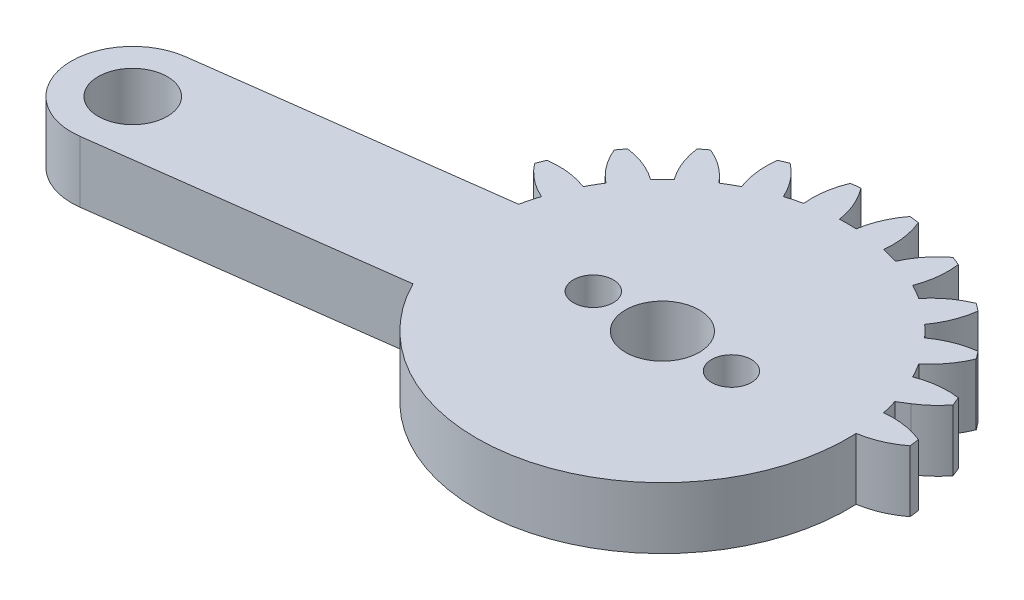
SolidWorks part; units mm, degrees
ref_plane "Front Plane" through (0, 0, 0) normal (0, 0, 1) x (1, 0, 0)
ref_plane "Top Plane" through (0, 0, 0) normal (0, 1, 0) x (1, 0, 0)
ref_plane "Right Plane" through (0, 0, 0) normal (1, 0, 0) x (0, 0, -1)
sketch "Sketch1" plane through (0, 0, 0) normal (0, 1, 0) x (1, 0, 0)
  line L0 (20.6437, 4) -> (2.0816, 4)
  line L1 (2.0816, -4) -> (20.6437, -4)
  arc A0 (2.0816, 4) -> (3.5217, 5.3071) centre (-0.7683, 8.5867) ccw
  arc A1 (3.5217, 5.3071) -> (3.2829, 5.8838) centre (-10.1063, 0) ccw
  arc A2 (3.2829, 5.8838) -> (0.6271, 5.5703) centre (2.5684, 0.5313) ccw
  arc A3 (0.6271, 5.5703) -> (0.0844, 6.5103) centre (-10.1063, 0) ccw
  arc A4 (0.0844, 6.5103) -> (1.6838, 8.6535) centre (-3.3089, 10.711) ccw
  arc A5 (1.6838, 8.6535) -> (1.3038, 9.1487) centre (-10.1063, 0) ccw
  arc A6 (1.3038, 9.1487) -> (-1.1803, 8.1585) centre (1.999, 3.7936) ccw
  arc A7 (-1.1803, 8.1585) -> (-1.9479, 8.926) centre (-10.1063, 0) ccw
  arc A8 (-1.9479, 8.926) -> (-0.9576, 11.4102) centre (-6.3127, 12.1053) ccw
  arc A9 (-0.9576, 11.4102) -> (-1.4528, 11.7901) centre (-10.1063, 0) ccw
  arc A10 (-1.4528, 11.7901) -> (-3.596, 10.1907) centre (0.6046, 6.7975) ccw
  arc A11 (-3.596, 10.1907) -> (-4.5361, 10.7334) centre (-10.1063, 0) ccw
  arc A12 (-4.5361, 10.7334) -> (-4.2225, 13.3892) centre (-9.5751, 12.6747) ccw
  arc A13 (-4.2225, 13.3892) -> (-4.7992, 13.6281) centre (-10.1063, 0) ccw
  arc A14 (-4.7992, 13.6281) -> (-6.4554, 11.5285) centre (-1.5196, 9.3381) ccw
  arc A15 (-6.4554, 11.5285) -> (-7.5039, 11.8094) centre (-10.1063, 0) ccw
  arc A16 (-7.5039, 11.8094) -> (-7.8884, 14.4558) centre (-12.8736, 12.3803) ccw
  arc A17 (-7.8884, 14.4558) -> (-8.5072, 14.5373) centre (-10.1063, 0) ccw
  arc A18 (-8.5072, 14.5373) -> (-9.5636, 12.0806) centre (-4.2291, 11.2423) ccw
  arc A19 (-9.5636, 12.0806) -> (-10.6491, 12.0806) centre (-10.1063, 0) ccw
  arc A20 (-10.6491, 12.0806) -> (-11.7054, 14.5373) centre (-15.9836, 11.2423) ccw
  arc A21 (-11.7054, 14.5373) -> (-12.3243, 14.4558) centre (-10.1063, 0) ccw
  arc A22 (-12.3243, 14.4558) -> (-12.7088, 11.8094) centre (-7.3391, 12.3803) ccw
  arc A23 (-12.7088, 11.8094) -> (-13.7573, 11.5285) centre (-10.1063, 0) ccw
  arc A24 (-13.7573, 11.5285) -> (-15.4135, 13.6281) centre (-18.6931, 9.3381) ccw
  arc A25 (-15.4135, 13.6281) -> (-15.9901, 13.3892) centre (-10.1063, 0) ccw
  arc A26 (-15.9901, 13.3892) -> (-15.6766, 10.7334) centre (-10.6376, 12.6747) ccw
  arc A27 (-15.6766, 10.7334) -> (-16.6166, 10.1907) centre (-10.1063, 0) ccw
  arc A28 (-16.6166, 10.1907) -> (-18.7599, 11.7901) centre (-20.8173, 6.7975) ccw
  arc A29 (-18.7599, 11.7901) -> (-19.255, 11.4102) centre (-10.1063, 0) ccw
  arc A30 (-19.255, 11.4102) -> (-18.2648, 8.926) centre (-13.9, 12.1053) ccw
  arc A31 (-18.2648, 8.926) -> (-19.0324, 8.1585) centre (-10.1063, 0) ccw
  arc A32 (-19.0324, 8.1585) -> (-21.5165, 9.1487) centre (-22.2117, 3.7936) ccw
  arc A33 (-21.5165, 9.1487) -> (-21.8965, 8.6535) centre (-10.1063, 0) ccw
  arc A34 (-21.8965, 8.6535) -> (-20.2971, 6.5103) centre (-16.9038, 10.711) ccw
  arc A35 (-20.2971, 6.5103) -> (-20.8398, 5.5703) centre (-10.1063, 0) ccw
  arc A36 (-20.8398, 5.5703) -> (-23.4956, 5.8838) centre (-22.7811, 0.5313) ccw
  arc A37 (-23.4956, 5.8838) -> (-23.7344, 5.3071) centre (-10.1063, 0) ccw
  arc A38 (-23.7344, 5.3071) -> (-21.6348, 3.6509) centre (-19.4444, 8.5867) ccw
  arc A39 (-21.6348, 3.6509) -> (-21.9157, 2.6025) centre (-10.1063, 0) ccw
  arc A40 (-21.9157, 2.6025) -> (-24.5622, 2.2179) centre (-22.4867, -2.7673) ccw
  arc A41 (-24.5622, 2.2179) -> (-24.6437, 1.5991) centre (-10.1063, 0) ccw
  arc A42 (-24.6437, 1.5991) -> (-22.1869, 0.5427) centre (-21.3486, 5.8773) ccw
  arc A43 (-22.1869, 0.5427) -> (-22.1869, -0.5427) centre (-10.1063, 0) ccw
  arc A44 (-22.1869, -0.5427) -> (-24.6437, -1.5991) centre (-21.3486, -5.8773) ccw
  arc A45 (-24.6437, -1.5991) -> (-24.5622, -2.2179) centre (-10.1063, 0) ccw
  arc A46 (-24.5622, -2.2179) -> (-21.9157, -2.6025) centre (-22.4867, 2.7673) ccw
  arc A47 (-21.9157, -2.6025) -> (-21.6348, -3.6509) centre (-10.1063, 0) ccw
  arc A48 (-21.6348, -3.6509) -> (-23.7344, -5.3071) centre (-19.4444, -8.5867) ccw
  arc A49 (-23.7344, -5.3071) -> (-23.4956, -5.8838) centre (-10.1063, 0) ccw
  arc A50 (-23.4956, -5.8838) -> (-20.8398, -5.5703) centre (-22.7811, -0.5313) ccw
  arc A51 (-20.8398, -5.5703) -> (-20.2971, -6.5103) centre (-10.1063, 0) ccw
  arc A52 (-20.2971, -6.5103) -> (-21.8965, -8.6535) centre (-16.9038, -10.711) ccw
  arc A53 (-21.8965, -8.6535) -> (-21.5165, -9.1487) centre (-10.1063, 0) ccw
  arc A54 (-21.5165, -9.1487) -> (-19.0324, -8.1585) centre (-22.2117, -3.7936) ccw
  arc A55 (-19.0324, -8.1585) -> (-18.2648, -8.926) centre (-10.1063, 0) ccw
  arc A56 (-18.2648, -8.926) -> (-19.255, -11.4102) centre (-13.9, -12.1053) ccw
  arc A57 (-19.255, -11.4102) -> (-18.7599, -11.7901) centre (-10.1063, 0) ccw
  arc A58 (-18.7599, -11.7901) -> (-16.6166, -10.1907) centre (-20.8173, -6.7975) ccw
  arc A59 (-16.6166, -10.1907) -> (-15.6766, -10.7334) centre (-10.1063, 0) ccw
  arc A60 (-15.6766, -10.7334) -> (-15.9901, -13.3892) centre (-10.6376, -12.6747) ccw
  arc A61 (-15.9901, -13.3892) -> (-15.4135, -13.6281) centre (-10.1063, 0) ccw
  arc A62 (-15.4135, -13.6281) -> (-13.7573, -11.5285) centre (-18.6931, -9.3381) ccw
  arc A63 (-13.7573, -11.5285) -> (-12.7088, -11.8094) centre (-10.1063, 0) ccw
  arc A64 (-12.7088, -11.8094) -> (-12.3243, -14.4558) centre (-7.3391, -12.3803) ccw
  arc A65 (-12.3243, -14.4558) -> (-11.7054, -14.5373) centre (-10.1063, 0) ccw
  arc A66 (-11.7054, -14.5373) -> (-10.6491, -12.0806) centre (-15.9836, -11.2423) ccw
  arc A67 (-10.6491, -12.0806) -> (-9.5636, -12.0806) centre (-10.1063, 0) ccw
  arc A68 (-9.5636, -12.0806) -> (-8.5072, -14.5373) centre (-4.2291, -11.2423) ccw
  arc A69 (-8.5072, -14.5373) -> (-7.8884, -14.4558) centre (-10.1063, 0) ccw
  arc A70 (-7.8884, -14.4558) -> (-7.5039, -11.8094) centre (-12.8736, -12.3803) ccw
  arc A71 (-7.5039, -11.8094) -> (-6.4554, -11.5285) centre (-10.1063, 0) ccw
  arc A72 (-6.4554, -11.5285) -> (-4.7992, -13.6281) centre (-1.5196, -9.3381) ccw
  arc A73 (-4.7992, -13.6281) -> (-4.2225, -13.3892) centre (-10.1063, 0) ccw
  arc A74 (-4.2225, -13.3892) -> (-4.5361, -10.7334) centre (-9.5751, -12.6747) ccw
  arc A75 (-4.5361, -10.7334) -> (-3.596, -10.1907) centre (-10.1063, 0) ccw
  arc A76 (-3.596, -10.1907) -> (-1.4528, -11.7901) centre (0.6046, -6.7975) ccw
  arc A77 (-1.4528, -11.7901) -> (-0.9576, -11.4102) centre (-10.1063, 0) ccw
  arc A78 (-0.9576, -11.4102) -> (-1.9479, -8.926) centre (-6.3127, -12.1053) ccw
  arc A79 (-1.9479, -8.926) -> (-1.1803, -8.1585) centre (-10.1063, 0) ccw
  arc A80 (-1.1803, -8.1585) -> (1.3038, -9.1487) centre (1.999, -3.7936) ccw
  arc A81 (1.3038, -9.1487) -> (1.6838, -8.6535) centre (-10.1063, 0) ccw
  arc A82 (1.6838, -8.6535) -> (0.0844, -6.5103) centre (-3.3089, -10.711) ccw
  arc A83 (0.0844, -6.5103) -> (0.6271, -5.5703) centre (-10.1063, 0) ccw
  arc A84 (0.6271, -5.5703) -> (3.2829, -5.8838) centre (2.5684, -0.5313) ccw
  arc A85 (3.2829, -5.8838) -> (3.5217, -5.3071) centre (-10.1063, 0) ccw
  arc A86 (3.5217, -5.3071) -> (2.0816, -4) centre (-0.7683, -8.5867) ccw
  arc A87 (20.6437, -4) -> (20.6437, 4) centre (20.6437, 0) ccw
  circle A88 centre (-10.1063, 0) radius 1.5
  circle A89 centre (20.6437, 0) radius 2.25
  dimension "D1" = 3
  dimension "D2" = 4.5
extrude "Boss-Extrude1" add sketch "Sketch1" along normal blind 4
sketch "Sketch3" plane through (0, 4, 0) normal (0, 1, 0) x (1, 0, 0)
  line L0 (-10.1063, 0) -> (-40.8563, 0) construction
  line L1 (-10.1063, 0) -> (-40.5933, -4.0137)
  line L2 (-10.6284, 3.9658) -> (-41.1154, -0.0479)
  line L3 (-9.5842, -3.9658) -> (-40.0712, -7.9795)
  line L4 (-10.1063, 0) -> (-4.5096, 13.5117) construction
  line L5 (-10.1063, 0) -> (-8.1974, 14.4999) construction
  circle A0 centre (-10.1063, 0) radius 1.5
  circle A1 centre (20.6437, 0) radius 2.25 construction
  circle A2 centre (20.6437, 0) radius 2.25
  circle A3 centre (-40.5933, -4.0137) radius 2.25
  circle A4 centre (-40.5933, -4.0137) radius 4
  circle A5 centre (-10.1063, 0) radius 4
  arc A6 (-4.2225, 13.3892) -> (-4.7992, 13.6281) centre (-10.1063, 0) ccw construction
  arc A7 (-7.8884, 14.4558) -> (-8.5072, 14.5373) centre (-10.1063, 0) ccw construction
  dimension "D2" = 3
  dimension "D5" = 4.5
  dimension "D6" = 8
  dimension "D7" = 8
  dimension "D1" = 30.75
  dimension "D4" = 7.5
extrude "Boss-Extrude2" add sketch "Sketch3" against normal blind 4
sketch "Sketch4" plane through (0, 4, 0) normal (0, 1, 0) x (1, 0, 0)
  line L0 (20.6437, 4) -> (2.0816, 4) construction
  line L1 (2.0816, -4) -> (20.6437, -4) construction
  line L2 (20.6437, 4) -> (2.0816, 4)
  line L3 (2.0816, -4) -> (20.6437, -4)
  line L4 (2.0816, 4) -> (1.4381, 3.6001)
  line L5 (-21.6245, -5.5509) -> (-20.8986, -5.4553)
  line L6 (-10.1063, 0) -> (0.0844, 6.5103) construction
  line L7 (-10.1063, 0) -> (1.9742, 0.5427) construction
  line L8 (-24.5755, 2.1296) -> (-41.1154, -0.0479)
  line L9 (-40.0712, -7.9795) -> (-23.5312, -5.8019)
  line L10 (2.0816, -4) -> (20.6437, -4)
  line L11 (20.6437, 4) -> (2.0816, 4)
  line L12 (-21.9429, 2.4762) -> (-41.1154, -0.0479)
  line L13 (-40.0712, -7.9795) -> (-21.6245, -5.5509)
  line L14 (2.0816, -4) -> (20.6437, -4)
  line L15 (20.6437, 4) -> (2.0816, 4)
  circle A0 centre (-10.1063, 0) radius 12.0927
  arc A1 (3.2829, 5.8838) -> (0.6271, 5.5703) centre (2.5684, 0.5313) ccw construction
  arc A2 (3.5217, 5.3071) -> (3.2829, 5.8838) centre (-10.1063, 0) ccw construction
  arc A3 (2.0816, 4) -> (3.5217, 5.3071) centre (-0.7683, 8.5867) ccw construction
  arc A4 (20.6437, -4) -> (20.6437, 4) centre (20.6437, 0) ccw construction
  arc A5 (3.5217, -5.3071) -> (2.0816, -4) centre (-0.7683, -8.5867) ccw construction
  arc A6 (3.2829, -5.8838) -> (3.5217, -5.3071) centre (-10.1063, 0) ccw construction
  arc A7 (0.6271, -5.5703) -> (3.2829, -5.8838) centre (2.5684, -0.5313) ccw construction
  arc A8 (3.2829, 5.8838) -> (0.6271, 5.5703) centre (2.5684, 0.5313) ccw
  arc A9 (3.5217, 5.3071) -> (3.2829, 5.8838) centre (-10.1063, 0) ccw
  arc A10 (2.0816, 4) -> (3.5217, 5.3071) centre (-0.7683, 8.5867) ccw
  arc A11 (20.6437, -4) -> (20.6437, 4) centre (20.6437, 0) ccw
  arc A12 (3.5217, -5.3071) -> (2.0816, -4) centre (-0.7683, -8.5867) ccw
  arc A13 (3.2829, -5.8838) -> (3.5217, -5.3071) centre (-10.1063, 0) ccw
  arc A14 (0.6271, -5.5703) -> (3.2829, -5.8838) centre (2.5684, -0.5313) ccw
  arc A15 (1.9742, 0.5427) -> (4.431, 1.5991) centre (1.1359, 5.8773) ccw
  arc A16 (4.3495, 2.2179) -> (1.7031, 2.6025) centre (2.274, -2.7673) ccw
  arc A17 (4.431, 1.5991) -> (4.3495, 2.2179) centre (-10.1063, 0) ccw
  arc A95 (-21.6348, 3.6509) -> (-21.9157, 2.6025) centre (-10.1063, 0) ccw
  arc A96 (-41.1154, -0.0479) -> (-40.0712, -7.9795) centre (-40.5933, -4.0137) ccw
  arc A97 (-20.2971, -6.5103) -> (-21.8965, -8.6535) centre (-16.9038, -10.711) ccw
  arc A98 (-21.8965, -8.6535) -> (-21.5165, -9.1487) centre (-10.1063, 0) ccw
  arc A99 (-21.5165, -9.1487) -> (-19.0324, -8.1585) centre (-22.2117, -3.7936) ccw
  arc A100 (-19.0324, -8.1585) -> (-18.2648, -8.926) centre (-10.1063, 0) ccw
  arc A101 (-18.2648, -8.926) -> (-19.255, -11.4102) centre (-13.9, -12.1053) ccw
  arc A102 (-19.255, -11.4102) -> (-18.7599, -11.7901) centre (-10.1063, 0) ccw
  arc A103 (-18.7599, -11.7901) -> (-16.6166, -10.1907) centre (-20.8173, -6.7975) ccw
  arc A104 (-16.6166, -10.1907) -> (-15.6766, -10.7334) centre (-10.1063, 0) ccw
  arc A105 (-15.6766, -10.7334) -> (-15.9901, -13.3892) centre (-10.6376, -12.6747) ccw
  arc A106 (-15.9901, -13.3892) -> (-15.4135, -13.6281) centre (-10.1063, 0) ccw
  arc A107 (-15.4135, -13.6281) -> (-13.7573, -11.5285) centre (-18.6931, -9.3381) ccw
  arc A108 (-13.7573, -11.5285) -> (-12.7088, -11.8094) centre (-10.1063, 0) ccw
  arc A109 (-12.7088, -11.8094) -> (-12.3243, -14.4558) centre (-7.3391, -12.3803) ccw
  arc A110 (-12.3243, -14.4558) -> (-11.7054, -14.5373) centre (-10.1063, 0) ccw
  arc A111 (-11.7054, -14.5373) -> (-10.6491, -12.0806) centre (-15.9836, -11.2423) ccw
  arc A112 (-10.6491, -12.0806) -> (-9.5636, -12.0806) centre (-10.1063, 0) ccw
  arc A113 (-9.5636, -12.0806) -> (-8.5072, -14.5373) centre (-4.2291, -11.2423) ccw
  arc A114 (-8.5072, -14.5373) -> (-7.8884, -14.4558) centre (-10.1063, 0) ccw
  arc A115 (-7.8884, -14.4558) -> (-7.5039, -11.8094) centre (-12.8736, -12.3803) ccw
  arc A116 (-7.5039, -11.8094) -> (-6.4554, -11.5285) centre (-10.1063, 0) ccw
  arc A117 (-6.4554, -11.5285) -> (-4.7992, -13.6281) centre (-1.5196, -9.3381) ccw
  arc A118 (-4.7992, -13.6281) -> (-4.2225, -13.3892) centre (-10.1063, 0) ccw
  arc A119 (-4.2225, -13.3892) -> (-4.5361, -10.7334) centre (-9.5751, -12.6747) ccw
  arc A120 (-4.5361, -10.7334) -> (-3.596, -10.1907) centre (-10.1063, 0) ccw
  arc A121 (-3.596, -10.1907) -> (-1.4528, -11.7901) centre (0.6046, -6.7975) ccw
  arc A122 (-1.4528, -11.7901) -> (-0.9576, -11.4102) centre (-10.1063, 0) ccw
  arc A123 (-0.9576, -11.4102) -> (-1.9479, -8.926) centre (-6.3127, -12.1053) ccw
  arc A124 (-1.9479, -8.926) -> (-1.1803, -8.1585) centre (-10.1063, 0) ccw
  arc A125 (-1.1803, -8.1585) -> (1.3038, -9.1487) centre (1.999, -3.7936) ccw
  arc A126 (1.3038, -9.1487) -> (1.6838, -8.6535) centre (-10.1063, 0) ccw
  arc A127 (1.6838, -8.6535) -> (0.0844, -6.5103) centre (-3.3089, -10.711) ccw
  arc A128 (0.0844, -6.5103) -> (0.6271, -5.5703) centre (-10.1063, 0) ccw
  arc A129 (0.6271, -5.5703) -> (3.2829, -5.8838) centre (2.5684, -0.5313) ccw
  arc A130 (3.2829, -5.8838) -> (3.5217, -5.3071) centre (-10.1063, 0) ccw
  arc A131 (3.5217, -5.3071) -> (2.0816, -4) centre (-0.7683, -8.5867) ccw
  arc A132 (20.6437, -4) -> (20.6437, 4) centre (20.6437, 0) ccw
  arc A133 (2.0816, 4) -> (3.5217, 5.3071) centre (-0.7683, 8.5867) ccw
  arc A134 (3.5217, 5.3071) -> (3.2829, 5.8838) centre (-10.1063, 0) ccw
  arc A135 (3.2829, 5.8838) -> (0.6271, 5.5703) centre (2.5684, 0.5313) ccw
  arc A136 (0.6271, 5.5703) -> (0.0844, 6.5103) centre (-10.1063, 0) ccw
  arc A137 (0.0844, 6.5103) -> (1.6838, 8.6535) centre (-3.3089, 10.711) ccw
  arc A138 (1.6838, 8.6535) -> (1.3038, 9.1487) centre (-10.1063, 0) ccw
  arc A139 (1.3038, 9.1487) -> (-1.1803, 8.1585) centre (1.999, 3.7936) ccw
  arc A140 (-1.1803, 8.1585) -> (-1.9479, 8.926) centre (-10.1063, 0) ccw
  arc A141 (-1.9479, 8.926) -> (-0.9576, 11.4102) centre (-6.3127, 12.1053) ccw
  arc A142 (-0.9576, 11.4102) -> (-1.4528, 11.7901) centre (-10.1063, 0) ccw
  arc A143 (-1.4528, 11.7901) -> (-3.596, 10.1907) centre (0.6046, 6.7975) ccw
  arc A144 (-3.596, 10.1907) -> (-4.5361, 10.7334) centre (-10.1063, 0) ccw
  arc A145 (-4.5361, 10.7334) -> (-4.2225, 13.3892) centre (-9.5751, 12.6747) ccw
  arc A146 (-4.2225, 13.3892) -> (-4.7992, 13.6281) centre (-10.1063, 0) ccw
  arc A147 (-4.7992, 13.6281) -> (-6.4554, 11.5285) centre (-1.5196, 9.3381) ccw
  arc A148 (-6.4554, 11.5285) -> (-7.5039, 11.8094) centre (-10.1063, 0) ccw
  arc A149 (-7.5039, 11.8094) -> (-7.8884, 14.4558) centre (-12.8736, 12.3803) ccw
  arc A150 (-7.8884, 14.4558) -> (-8.5072, 14.5373) centre (-10.1063, 0) ccw
  arc A151 (-8.5072, 14.5373) -> (-9.5636, 12.0806) centre (-4.2291, 11.2423) ccw
  arc A152 (-9.5636, 12.0806) -> (-10.6491, 12.0806) centre (-10.1063, 0) ccw
  arc A153 (-10.6491, 12.0806) -> (-11.7054, 14.5373) centre (-15.9836, 11.2423) ccw
  arc A154 (-11.7054, 14.5373) -> (-12.3243, 14.4558) centre (-10.1063, 0) ccw
  arc A155 (-12.3243, 14.4558) -> (-12.7088, 11.8094) centre (-7.3391, 12.3803) ccw
  arc A156 (-12.7088, 11.8094) -> (-13.7573, 11.5285) centre (-10.1063, 0) ccw
  arc A157 (-13.7573, 11.5285) -> (-15.4135, 13.6281) centre (-18.6931, 9.3381) ccw
  arc A158 (-15.4135, 13.6281) -> (-15.9901, 13.3892) centre (-10.1063, 0) ccw
  arc A159 (-15.9901, 13.3892) -> (-15.6766, 10.7334) centre (-10.6376, 12.6747) ccw
  arc A160 (-15.6766, 10.7334) -> (-16.6166, 10.1907) centre (-10.1063, 0) ccw
  arc A161 (-16.6166, 10.1907) -> (-18.7599, 11.7901) centre (-20.8173, 6.7975) ccw
  arc A162 (-18.7599, 11.7901) -> (-19.255, 11.4102) centre (-10.1063, 0) ccw
  arc A163 (-19.255, 11.4102) -> (-18.2648, 8.926) centre (-13.9, 12.1053) ccw
  arc A164 (-18.2648, 8.926) -> (-19.0324, 8.1585) centre (-10.1063, 0) ccw
  arc A165 (-19.0324, 8.1585) -> (-21.5165, 9.1487) centre (-22.2117, 3.7936) ccw
  arc A166 (-21.5165, 9.1487) -> (-21.8965, 8.6535) centre (-10.1063, 0) ccw
  arc A167 (-21.8965, 8.6535) -> (-20.2971, 6.5103) centre (-16.9038, 10.711) ccw
  arc A168 (-20.2971, 6.5103) -> (-20.8398, 5.5703) centre (-10.1063, 0) ccw
  arc A169 (-20.8398, 5.5703) -> (-23.4956, 5.8838) centre (-22.7811, 0.5313) ccw
  arc A170 (-23.4956, 5.8838) -> (-23.7344, 5.3071) centre (-10.1063, 0) ccw
  arc A171 (-23.7344, 5.3071) -> (-21.6348, 3.6509) centre (-19.4444, 8.5867) ccw
  arc A172 (-21.6348, 3.6509) -> (-21.9157, 2.6025) centre (-10.1063, 0) ccw
  arc A175 (-23.4956, -5.8838) -> (-20.8398, -5.5703) centre (-22.7811, -0.5313) ccw
  arc A176 (-41.1154, -0.0479) -> (-40.0712, -7.9795) centre (-40.5933, -4.0137) ccw
  arc A177 (-20.2971, -6.5103) -> (-21.8965, -8.6535) centre (-16.9038, -10.711) ccw
  arc A178 (-21.8965, -8.6535) -> (-21.5165, -9.1487) centre (-10.1063, 0) ccw
  arc A179 (-21.5165, -9.1487) -> (-19.0324, -8.1585) centre (-22.2117, -3.7936) ccw
  arc A180 (-19.0324, -8.1585) -> (-18.2648, -8.926) centre (-10.1063, 0) ccw
  arc A181 (-18.2648, -8.926) -> (-19.255, -11.4102) centre (-13.9, -12.1053) ccw
  arc A182 (-19.255, -11.4102) -> (-18.7599, -11.7901) centre (-10.1063, 0) ccw
  arc A183 (-18.7599, -11.7901) -> (-16.6166, -10.1907) centre (-20.8173, -6.7975) ccw
  arc A184 (-16.6166, -10.1907) -> (-15.6766, -10.7334) centre (-10.1063, 0) ccw
  arc A185 (-15.6766, -10.7334) -> (-15.9901, -13.3892) centre (-10.6376, -12.6747) ccw
  arc A186 (-15.9901, -13.3892) -> (-15.4135, -13.6281) centre (-10.1063, 0) ccw
  arc A187 (-15.4135, -13.6281) -> (-13.7573, -11.5285) centre (-18.6931, -9.3381) ccw
  arc A188 (-13.7573, -11.5285) -> (-12.7088, -11.8094) centre (-10.1063, 0) ccw
  arc A189 (-12.7088, -11.8094) -> (-12.3243, -14.4558) centre (-7.3391, -12.3803) ccw
  arc A190 (-12.3243, -14.4558) -> (-11.7054, -14.5373) centre (-10.1063, 0) ccw
  arc A191 (-11.7054, -14.5373) -> (-10.6491, -12.0806) centre (-15.9836, -11.2423) ccw
  arc A192 (-10.6491, -12.0806) -> (-9.5636, -12.0806) centre (-10.1063, 0) ccw
  arc A193 (-9.5636, -12.0806) -> (-8.5072, -14.5373) centre (-4.2291, -11.2423) ccw
  arc A194 (-8.5072, -14.5373) -> (-7.8884, -14.4558) centre (-10.1063, 0) ccw
  arc A195 (-7.8884, -14.4558) -> (-7.5039, -11.8094) centre (-12.8736, -12.3803) ccw
  arc A196 (-7.5039, -11.8094) -> (-6.4554, -11.5285) centre (-10.1063, 0) ccw
  arc A197 (-6.4554, -11.5285) -> (-4.7992, -13.6281) centre (-1.5196, -9.3381) ccw
  arc A198 (-4.7992, -13.6281) -> (-4.2225, -13.3892) centre (-10.1063, 0) ccw
  arc A199 (-4.2225, -13.3892) -> (-4.5361, -10.7334) centre (-9.5751, -12.6747) ccw
  arc A200 (-4.5361, -10.7334) -> (-3.596, -10.1907) centre (-10.1063, 0) ccw
  arc A201 (-3.596, -10.1907) -> (-1.4528, -11.7901) centre (0.6046, -6.7975) ccw
  arc A202 (-1.4528, -11.7901) -> (-0.9576, -11.4102) centre (-10.1063, 0) ccw
  arc A203 (-0.9576, -11.4102) -> (-1.9479, -8.926) centre (-6.3127, -12.1053) ccw
  arc A204 (-1.9479, -8.926) -> (-1.1803, -8.1585) centre (-10.1063, 0) ccw
  arc A205 (-1.1803, -8.1585) -> (1.3038, -9.1487) centre (1.999, -3.7936) ccw
  arc A206 (1.3038, -9.1487) -> (1.6838, -8.6535) centre (-10.1063, 0) ccw
  arc A207 (1.6838, -8.6535) -> (0.0844, -6.5103) centre (-3.3089, -10.711) ccw
  arc A208 (0.0844, -6.5103) -> (0.6271, -5.5703) centre (-10.1063, 0) ccw
  arc A209 (0.6271, -5.5703) -> (3.2829, -5.8838) centre (2.5684, -0.5313) ccw
  arc A210 (3.2829, -5.8838) -> (3.5217, -5.3071) centre (-10.1063, 0) ccw
  arc A211 (3.5217, -5.3071) -> (2.0816, -4) centre (-0.7683, -8.5867) ccw
  arc A212 (20.6437, -4) -> (20.6437, 4) centre (20.6437, 0) ccw
  arc A213 (2.0816, 4) -> (3.5217, 5.3071) centre (-0.7683, 8.5867) ccw
  arc A214 (3.5217, 5.3071) -> (3.2829, 5.8838) centre (-10.1063, 0) ccw
  arc A215 (3.2829, 5.8838) -> (0.6271, 5.5703) centre (2.5684, 0.5313) ccw
  arc A216 (0.6271, 5.5703) -> (0.0844, 6.5103) centre (-10.1063, 0) ccw
  arc A217 (0.0844, 6.5103) -> (1.6838, 8.6535) centre (-3.3089, 10.711) ccw
  arc A218 (1.6838, 8.6535) -> (1.3038, 9.1487) centre (-10.1063, 0) ccw
  arc A219 (1.3038, 9.1487) -> (-1.1803, 8.1585) centre (1.999, 3.7936) ccw
  arc A220 (-1.1803, 8.1585) -> (-1.9479, 8.926) centre (-10.1063, 0) ccw
  arc A221 (-1.9479, 8.926) -> (-0.9576, 11.4102) centre (-6.3127, 12.1053) ccw
  arc A222 (-0.9576, 11.4102) -> (-1.4528, 11.7901) centre (-10.1063, 0) ccw
  arc A223 (-1.4528, 11.7901) -> (-3.596, 10.1907) centre (0.6046, 6.7975) ccw
  arc A224 (-3.596, 10.1907) -> (-4.5361, 10.7334) centre (-10.1063, 0) ccw
  arc A225 (-4.5361, 10.7334) -> (-4.2225, 13.3892) centre (-9.5751, 12.6747) ccw
  arc A226 (-4.2225, 13.3892) -> (-4.7992, 13.6281) centre (-10.1063, 0) ccw
  arc A227 (-4.7992, 13.6281) -> (-6.4554, 11.5285) centre (-1.5196, 9.3381) ccw
  arc A228 (-6.4554, 11.5285) -> (-7.5039, 11.8094) centre (-10.1063, 0) ccw
  arc A229 (-7.5039, 11.8094) -> (-7.8884, 14.4558) centre (-12.8736, 12.3803) ccw
  arc A230 (-7.8884, 14.4558) -> (-8.5072, 14.5373) centre (-10.1063, 0) ccw
  arc A231 (-8.5072, 14.5373) -> (-9.5636, 12.0806) centre (-4.2291, 11.2423) ccw
  arc A232 (-9.5636, 12.0806) -> (-10.6491, 12.0806) centre (-10.1063, 0) ccw
  arc A233 (-10.6491, 12.0806) -> (-11.7054, 14.5373) centre (-15.9836, 11.2423) ccw
  arc A234 (-11.7054, 14.5373) -> (-12.3243, 14.4558) centre (-10.1063, 0) ccw
  arc A235 (-12.3243, 14.4558) -> (-12.7088, 11.8094) centre (-7.3391, 12.3803) ccw
  arc A236 (-12.7088, 11.8094) -> (-13.7573, 11.5285) centre (-10.1063, 0) ccw
  arc A237 (-13.7573, 11.5285) -> (-15.4135, 13.6281) centre (-18.6931, 9.3381) ccw
  arc A238 (-15.4135, 13.6281) -> (-15.9901, 13.3892) centre (-10.1063, 0) ccw
  arc A239 (-15.9901, 13.3892) -> (-15.6766, 10.7334) centre (-10.6376, 12.6747) ccw
  arc A240 (-15.6766, 10.7334) -> (-16.6166, 10.1907) centre (-10.1063, 0) ccw
  arc A241 (-16.6166, 10.1907) -> (-18.7599, 11.7901) centre (-20.8173, 6.7975) ccw
  arc A242 (-18.7599, 11.7901) -> (-19.255, 11.4102) centre (-10.1063, 0) ccw
  arc A243 (-19.255, 11.4102) -> (-18.2648, 8.926) centre (-13.9, 12.1053) ccw
  arc A244 (-18.2648, 8.926) -> (-19.0324, 8.1585) centre (-10.1063, 0) ccw
  arc A245 (-19.0324, 8.1585) -> (-21.5165, 9.1487) centre (-22.2117, 3.7936) ccw
  arc A246 (-21.5165, 9.1487) -> (-21.8965, 8.6535) centre (-10.1063, 0) ccw
  arc A247 (-21.8965, 8.6535) -> (-20.2971, 6.5103) centre (-16.9038, 10.711) ccw
  arc A248 (-20.2971, 6.5103) -> (-20.8398, 5.5703) centre (-10.1063, 0) ccw
  arc A249 (-20.8398, 5.5703) -> (-23.4956, 5.8838) centre (-22.7811, 0.5313) ccw
  arc A250 (-23.4956, 5.8838) -> (-23.7344, 5.3071) centre (-10.1063, 0) ccw
  arc A251 (-23.7344, 5.3071) -> (-21.6348, 3.6509) centre (-19.4444, 8.5867) ccw
  arc A252 (-23.4956, -5.8838) -> (-20.8398, -5.5703) centre (-22.7811, -0.5313) ccw
  arc A253 (-20.8398, -5.5703) -> (-20.2971, -6.5103) centre (-10.1063, 0) ccw
  arc A254 (-20.8398, -5.5703) -> (-20.2971, -6.5103) centre (-10.1063, 0) ccw
  arc A255 (-23.5312, -5.8019) -> (-23.4956, -5.8838) centre (-10.1063, 0) ccw
  arc A256 (-23.5312, -5.8019) -> (-23.4956, -5.8838) centre (-10.1063, 0) ccw
  arc A257 (-21.9157, 2.6025) -> (-24.5622, 2.2179) centre (-22.4867, -2.7673) ccw
  arc A258 (-21.9157, 2.6025) -> (-24.5622, 2.2179) centre (-22.4867, -2.7673) ccw
  arc A259 (-24.5622, 2.2179) -> (-24.5755, 2.1296) centre (-10.1063, 0) ccw
  arc A260 (-24.5622, 2.2179) -> (-24.5755, 2.1296) centre (-10.1063, 0) ccw
  point P40 (-10.1063, 0)
  dimension "D2" = 24.1855
  dimension "D4" = 30
  dimension "D1" = 0
  dimension "D3" = 2
extrude "Cut-Extrude1" cut sketch "Sketch4" against normal blind 4 contours A178 A179 A0 L5 A177 | A182 A183 A0 A181 | A186 A187 A0 A185 | A190 A191 A0 A189 | A194 A195 A0 A193 | A198 A199 A0 A197 | A202 A203 A0 A201 | A206 A207 A0 A205 | A258 A260 L12 A0 | L13 A256 A252 A0 L5 | A0 A14 A13 A12 L3 A11 L2 L4
sketch "Sketch5" plane through (0, 4, 0) normal (0, 1, 0) x (1, 0, 0)
  circle A0 centre (-10.1063, 0) radius 2.4
  circle A1 centre (-5.6063, 0) radius 1.3
  circle A2 centre (-14.6063, 0) radius 1.3
  circle A3 centre (-10.1063, 0) radius 1.5 construction
  dimension "D1" = 4.8
  dimension "D2" = 2.6
  dimension "D3" = 2.6
  dimension "D4" = 4.5
  dimension "D5" = 9
extrude "Cut-Extrude2" cut sketch "Sketch5" against normal up to next contours A2 | A1 | A0
